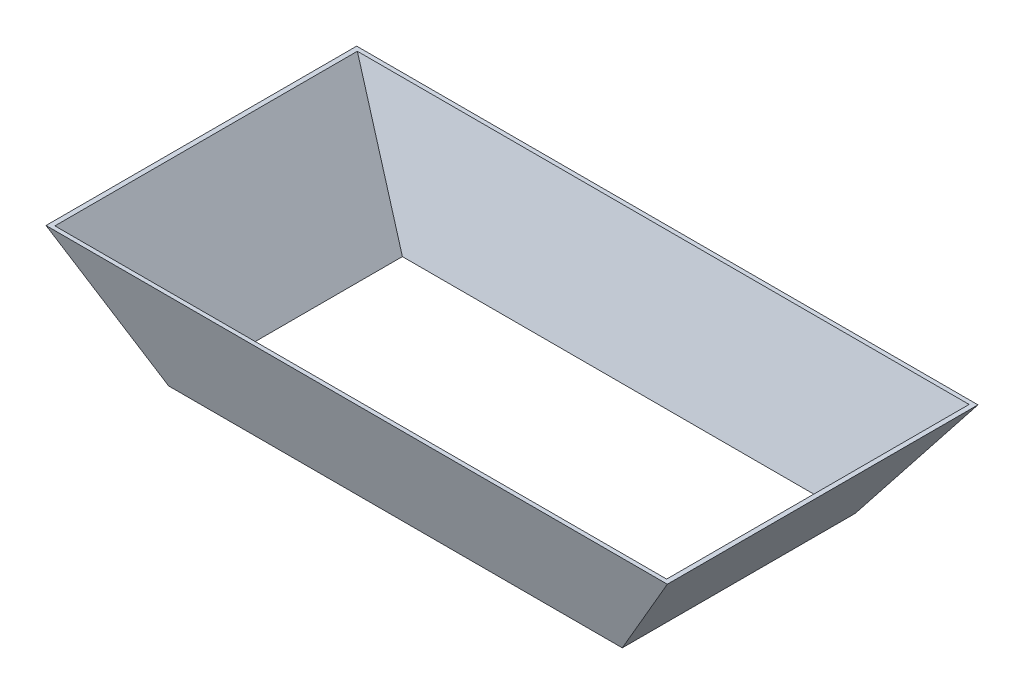
SolidWorks part; units mm, degrees
material "AISI 316 Stainless Steel Sheet (SS)"
ref_plane "Front Plane" through (0, 0, 0) normal (0, 0, 1) x (1, 0, 0)
ref_plane "Top Plane" through (0, 0, 0) normal (0, 1, 0) x (1, 0, 0)
ref_plane "Right Plane" through (0, 0, 0) normal (1, 0, 0) x (0, 0, -1)
sketch "Sketch1" plane through (0, 0, 0) normal (0, 1, 0) x (1, 0, 0)
  line L1 (292, 150) -> (-292, 150)
  line L2 (292, 150) -> (292, -150)
  line L3 (292, -150) -> (-292, -150)
  line L4 (-292, 150) -> (-292, -150)
  line L5 (292, 150) -> (-292, -150) construction
  line L6 (292, -150) -> (-292, 150) construction
  point P0 (0, 0)
  dimension "D1" = 300
  dimension "D2" = 584
ref_plane "Plane1" through (0, 150, 0) normal (0, 1, 0) x (1, 0, 0)
sketch "Sketch2" plane through (0, 150, 0) normal (0, 1, 0) x (1, 0, 0)
  line L1 (400, 200) -> (-400, 200)
  line L2 (400, 200) -> (400, -200)
  line L3 (400, -200) -> (-400, -200)
  line L4 (-400, 200) -> (-400, -200)
  line L5 (400, 200) -> (-400, -200) construction
  line L6 (400, -200) -> (-400, 200) construction
  point P0 (0, 0)
  dimension "D1" = 400
  dimension "D2" = 800
loft "Loft1" add profiles "Sketch2", "Sketch1"
shell "Shell1" thickness 5
